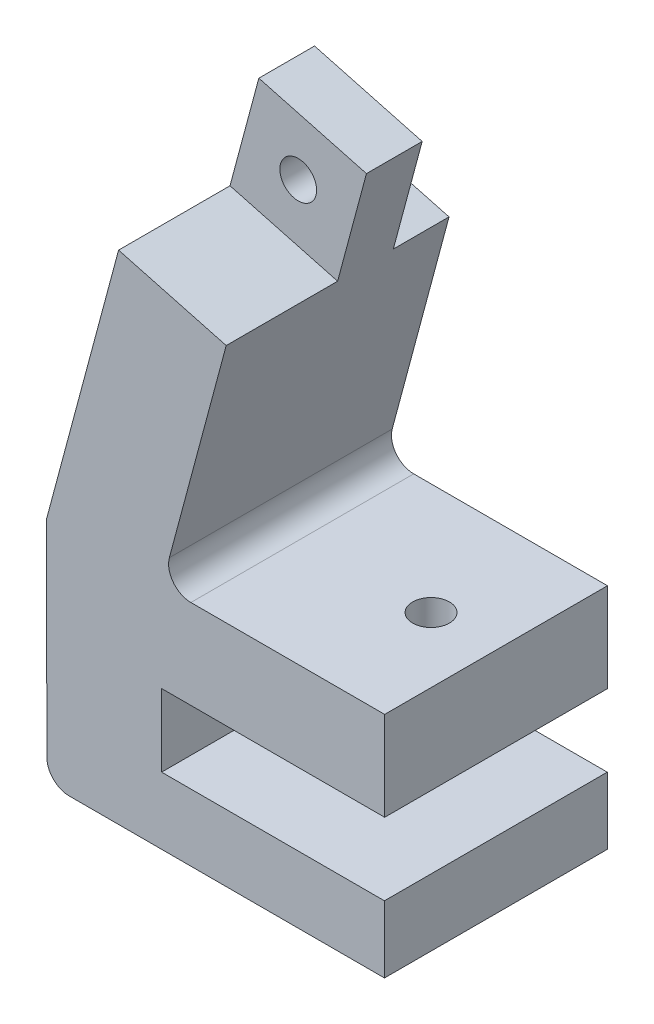
SolidWorks part; units mm, degrees
ref_plane "前视基准面" through (0, 0, 0) normal (0, 0, 1) x (1, 0, 0)
ref_plane "上视基准面" through (0, 0, 0) normal (0, 1, 0) x (1, 0, 0)
ref_plane "右视基准面" through (0, 0, 0) normal (1, 0, 0) x (0, 0, -1)
other "Configuration Table"
sketch "草图1" plane through (0, 0, 0) normal (0, 0, 1) x (1, 0, 0)
  line L0 (0.0201, -0.0524) -> (0.0169, 5.9476)
  line L1 (0.0169, 5.9476) -> (-19.9831, 5.9476)
  line L2 (-19.9831, 5.9476) -> (-20.0001, 12.4476)
  line L3 (-20.0001, 12.4476) -> (0.0376, 12.4476)
  line L4 (0.0376, 12.4476) -> (0.0376, 20.4476)
  line L5 (0.0376, 20.4476) -> (-19.9624, 20.4476)
  line L6 (-19.9624, 20.4476) -> (-11.5972, 51.6668)
  line L8 (-21.2565, 54.255) -> (-30.3152, 20.4476)
  line L9 (-30.3152, 20.4476) -> (-30.2797, -0.0524)
  line L10 (-30.2797, -0.0524) -> (0.0201, -0.0524)
  line L11 (-21.2565, 54.255) -> (-11.5972, 51.6668)
  line L19 (-19.9624, 20.4476) -> (-29.6217, 23.0358) construction
  point P2 (0, 0)
  point P9 (-3.8655, 42.1653)
  point P14 (-18.6198, 7.6724)
  dimension "D1" = 8
  dimension "D2" = 6
  dimension "D3" = 6.5
  dimension "D4" = 75
  dimension "D5" = 35
  dimension "D6" = 20
  dimension "D7" = 20
  dimension "D11" = 32.3205
extrude "凸台-拉伸1" add sketch "草图1" along normal blind 20
fillet "圆角1" radius 2 1 edges at (-19.9624, 20.4476, 10)
fillet "圆角2" radius 2 1 edges at (-30.2797, -0.0524, 10)
sketch "草图20" plane through (0, 0, 20) normal (0, 0, 1) x (1, 0, 0)
  line L0 (-11.5972, 51.6668) -> (-11.5972, 12.4476) construction
  line L1 (-20.0001, 12.4476) -> (0.0376, 12.4476) construction
sketch "草图22" plane through (0, 12.4476, 0) normal (0, -1, 0) x (1, 0, 0)
  line L1 (-11.5972, 20) -> (0, 20) construction
  line L2 (-11.5972, 20) -> (-11.5972, 0) construction
  line L3 (-11.5972, 0) -> (0, 0) construction
  line L4 (0, 20) -> (0, 0) construction
  line L5 (-11.5972, 20) -> (0, 0) construction
  line L6 (-11.5972, 0) -> (0, 20) construction
  point P4 (-5.7986, 10)
hole_wizard "M4 螺纹孔的螺纹孔钻头1" positions "草图29" profile "草图30" hole size "M4" standard "ISO"
sketch "草图29" plane through (0, 12.4476, 0) normal (0, -1, 0) x (-1, 0, 0)
  point P0 (5.7986, -10)
sketch "草图30" plane through (-5.7986, 12.4476, 10) normal (1, 0, 0) x (0, 0, -1)
  line L0 (0, 0) -> (0, 8)
  line L1 (0, 8) -> (1.65, 8)
  line L2 (1.65, 8) -> (1.65, 0)
  line L5 (1.65, 0) -> (0, 0)
  line L11 (0, -6.35) -> (0, 107.95) construction
  dimension "通孔孔直径" = 3.3
  dimension "通孔孔深度" = 8
sketch "草图31" plane through (0, 12.4476, 0) normal (0, -1, 0) x (1, 0, 0)
  line L0 (-11.5972, 0) -> (0, 20) construction
  circle A0 centre (-5.7986, 10) radius 3.5
extrude "切除-拉伸1" cut sketch "草图31" against normal blind 4
sketch "草图33" plane through (0, 0, 20) normal (0, 0, 1) x (1, 0, 0)
  line L0 (-21.2565, 54.255) -> (-11.5972, 51.6668)
  line L1 (-21.2565, 54.255) -> (-23.8447, 44.5958)
  line L2 (-11.5972, 51.6668) -> (-14.1854, 42.0076)
  line L3 (-23.8447, 44.5958) -> (-14.1854, 42.0076)
  line L4 (-21.2565, 54.255) -> (-14.1854, 42.0076) construction
  line L5 (-11.5972, 51.6668) -> (-23.8447, 44.5958) construction
  point P6 (-17.721, 48.1313)
  dimension "D1" = 10
extrude "切除-拉伸2" cut sketch "草图33" against normal blind 10
sketch "草图34" plane through (0, 0, 0) normal (0, 0, -1) x (-1, 0, 0)
  line L0 (11.5972, 51.6668) -> (21.2565, 54.255) construction
  line L1 (11.5972, 51.6668) -> (14.1854, 42.0076) construction
  line L2 (21.2565, 54.255) -> (23.8447, 44.5958) construction
  line L3 (14.1854, 42.0076) -> (23.8447, 44.5958) construction
  line L4 (11.5972, 51.6668) -> (23.8447, 44.5958) construction
  line L5 (21.2565, 54.255) -> (14.1854, 42.0076) construction
  circle A0 centre (17.721, 48.1313) radius 3.25
  point P6 (17.721, 48.1313)
  dimension "D2" = 6.5
  dimension "D1" = 10
extrude "切除-拉伸3" cut sketch "草图34" against normal blind 6
hole_wizard "M4 螺纹孔的螺纹孔钻头2" positions "草图37" profile "草图36" hole size "M4" standard "ISO" end condition up to next
sketch "草图37" plane through (0, 0, 6) normal (0, 0, -1) x (-1, 0, 0)
  point P0 (17.721, 48.1313)
sketch "草图36" plane through (-17.721, 48.1313, 6) normal (1, 0, 0) x (0, 1, 0)
  line L0 (0, 0) -> (0, 4)
  line L1 (0, 4) -> (1.65, 4)
  line L2 (1.65, 4) -> (1.65, 0)
  line L5 (1.65, 0) -> (0, 0)
  line L11 (0, -6.35) -> (0, 107.95) construction
  dimension "通孔孔直径" = 3.3
  dimension "通孔孔深度" = 4
sketch "草图38" plane through (-23.7371, 6.3603, 0) normal (0.9659, -0.2588, 0) x (0, 0, -1)
  line L1 (0, 46.9048) -> (-5, 46.9048)
  line L2 (0, 46.9048) -> (0, 36.9048)
  line L3 (0, 36.9048) -> (-5, 36.9048)
  line L4 (-5, 46.9048) -> (-5, 36.9048)
  line L5 (0, 46.9048) -> (-5, 36.9048) construction
  line L6 (0, 36.9048) -> (-5, 46.9048) construction
  point P4 (-2.5, 41.9048)
  dimension "D1" = 5
extrude "切除-拉伸4" cut sketch "草图38" against normal blind 11
